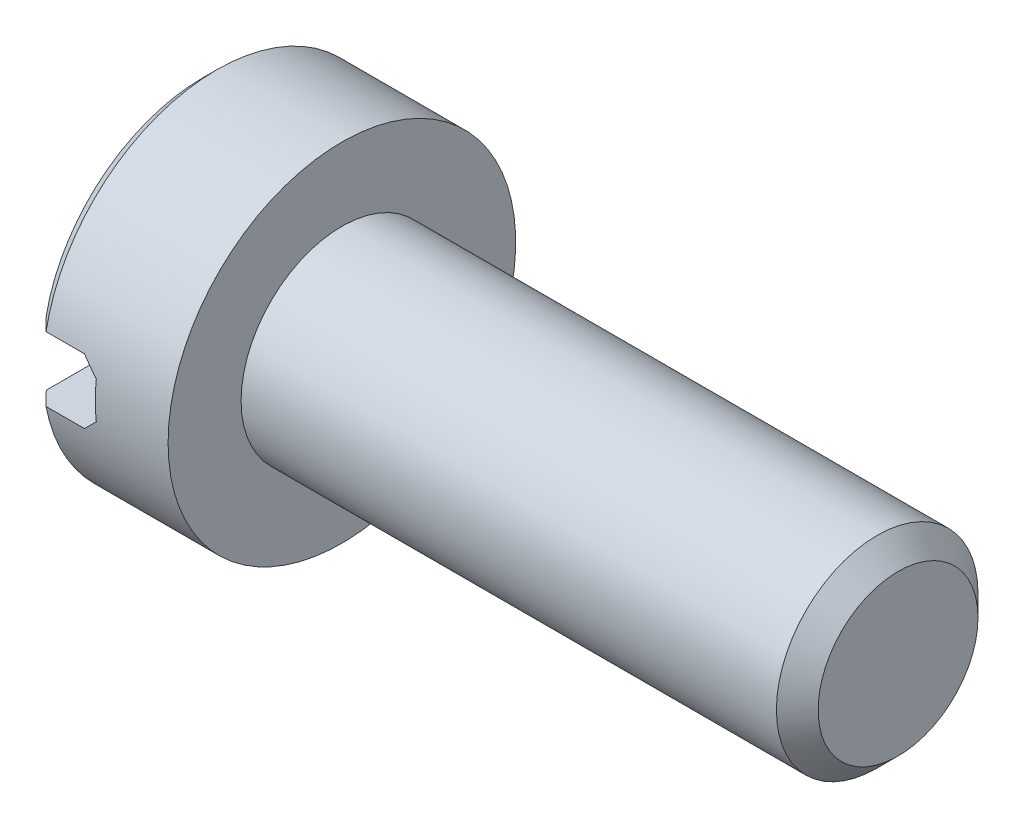
SolidWorks part; units mm, degrees
ref_plane "Face" through (0, 0, 0) normal (0, 0, 1) x (1, 0, 0)
ref_plane "Dessus" through (0, 0, 0) normal (0, 1, 0) x (1, 0, 0)
ref_plane "Droite" through (0, 0, 0) normal (1, 0, 0) x (0, 0, -1)
sketch "Esquisse1" plane through (0, 0, 0) normal (0, 0, 1) x (1, 0, 0)
  line L0 (0, 0) -> (0, 2.3)
  line L1 (0.2, 2.5) -> (2, 2.5)
  line L2 (2, 2.5) -> (2, 0)
  line L5 (0, 0) -> (7.6423, 0) construction
  line L7 (0, 2.3) -> (0.2, 2.5)
  line L8 (0, 0) -> (2, 0)
  point P1 (0, 2.5)
  dimension "D1" = 2.5
  dimension "D3" = 2
  dimension "D9" = 0.2
revolve "Révolution1" add sketch "Esquisse1" angle 360 about L5
sketch "Esquisse2" plane through (0, 0, 0) normal (0, 0, 1) x (1, 0, 0)
  line L0 (0, 2.3) -> (0, -2.3) construction
  line L1 (0, 0.4655) -> (0.7534, 0.4655)
  line L2 (0, 0.4655) -> (0, -0.4655)
  line L3 (0, -0.4655) -> (0.7534, -0.4655)
  line L4 (0.9534, 0.2655) -> (0.9534, -0.2655)
  line L5 (0.7534, 0.4655) -> (0.9534, 0.2655)
  line L6 (0.7534, -0.4655) -> (0.9534, -0.2655)
  point P1 (0.9534, -0.4655)
  point P3 (0.9534, 0.4655)
  dimension "D3" = 0.2
  dimension "D4" = 0.2
extrude "Enlèv. mat.-Extru.1" cut sketch "Esquisse2" against normal mid plane 10
sketch "Esquisse3" plane through (2, 0, 0) normal (1, 0, 0) x (0, 0, -1)
  circle A0 centre (0, 0) radius 1.45
extrude "Extrusion1" add sketch "Esquisse3" along normal blind 8
chamfer "Chanfrein1" distance 0.3 angle 45 1 edges at (10, 0, -1.45)
